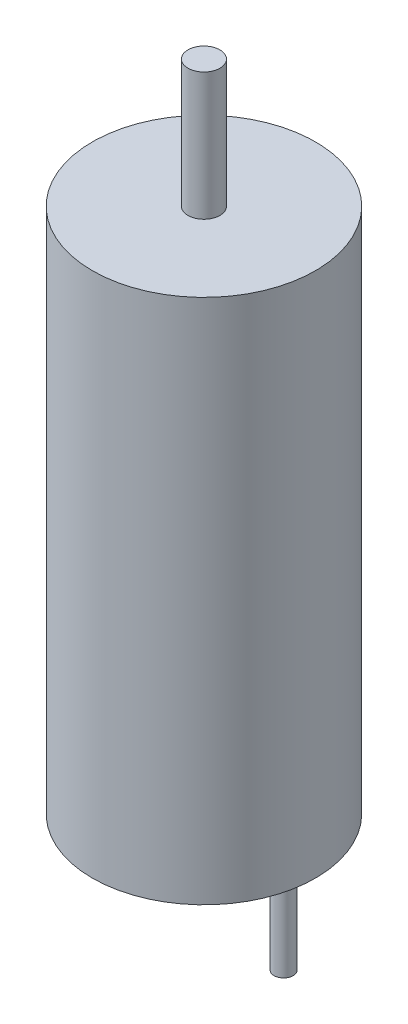
SolidWorks part; units mm, degrees
ref_plane "Front Plane" through (0, 0, 0) normal (0, 0, 1) x (1, 0, 0)
ref_plane "Top Plane" through (0, 0, 0) normal (0, 1, 0) x (1, 0, 0)
ref_plane "Right Plane" through (0, 0, 0) normal (1, 0, 0) x (0, 0, -1)
sketch "Sketch1" plane through (0, 0, 0) normal (0, 1, 0) x (1, 0, 0)
  circle A0 centre (0, 0) radius 3.5
  dimension "D1" = 7
extrude "Boss-Extrude1" add sketch "Sketch1" against normal blind 16.5
sketch "Sketch2" plane through (0, 0, 0) normal (0, 1, 0) x (1, 0, 0)
  circle A0 centre (0, 0) radius 0.5
extrude "Boss-Extrude2" add sketch "Sketch2" along normal blind 4
sketch "Sketch3" plane through (0, -16.5, 0) normal (0, -1, 0) x (1, 0, 0)
  line L0 (-3.5, 0) -> (3.5, 0) construction
  line L1 (0, -3.5) -> (0, 3.5) construction
  circle A0 centre (0, 0) radius 3.5 construction
  circle A2 centre (2.5, 0) radius 0.3
  circle A3 centre (-2.5, 0) radius 0.3
  dimension "D1" = 0.6
  dimension "D3" = 2.5
extrude "Boss-Extrude3" add sketch "Sketch3" along normal blind 3
